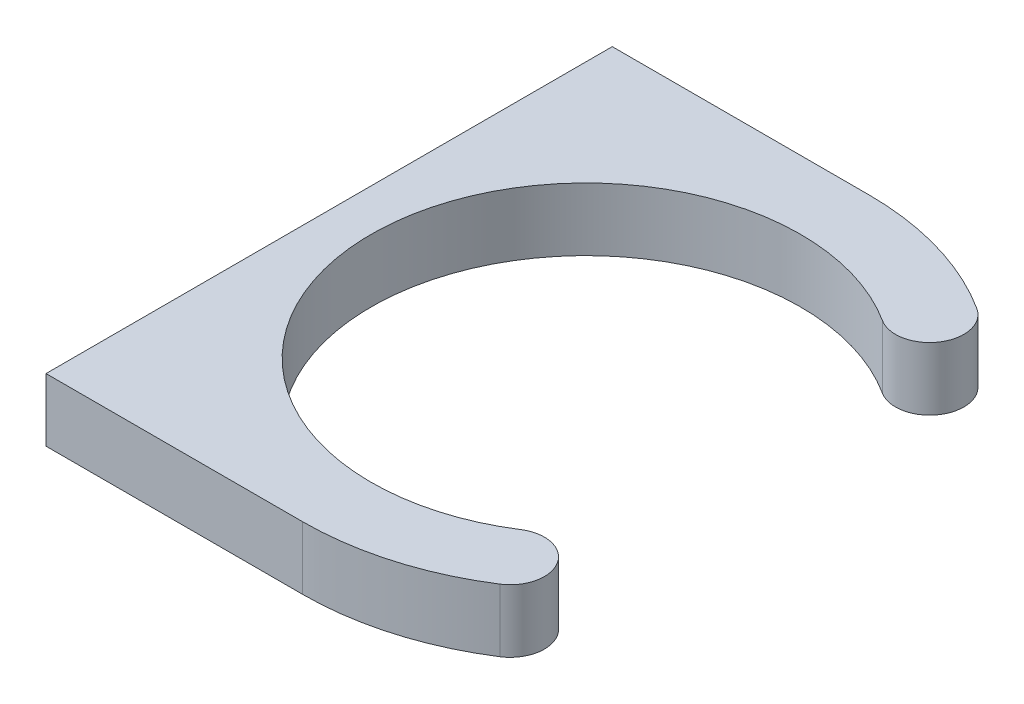
SolidWorks part; units mm, degrees
ref_plane "Front Plane" through (0, 0, 0) normal (0, 0, 1) x (1, 0, 0)
ref_plane "Top Plane" through (0, 0, 0) normal (0, 1, 0) x (1, 0, 0)
ref_plane "Right Plane" through (0, 0, 0) normal (1, 0, 0) x (0, 0, -1)
sketch "Sketch1" plane through (0, 0, 0) normal (0, 1, 0) x (1, 0, 0)
  line L0 (-38.862, 42.8625) -> (-38.862, -42.8625)
  line L1 (0, 42.8625) -> (-38.862, 42.8625)
  line L2 (0, -42.8625) -> (-38.862, -42.8625)
  circle A0 centre (0, 0) radius 32.512 construction
  arc A1 (23.0926, 36.1099) -> (0, 42.8625) centre (0, 0) ccw
  arc A2 (17.5161, 27.3901) -> (17.5161, -27.3901) centre (0, 0) ccw
  arc A3 (17.5161, 27.3901) -> (23.0926, 36.1099) centre (20.3043, 31.75) ccw
  arc A4 (17.5161, -27.3901) -> (23.0926, -36.1099) centre (20.3043, -31.75) cw
  arc A5 (0, -42.8625) -> (23.0926, -36.1099) centre (0, 0) ccw
  circle A6 centre (0, 0) radius 42.8625 construction
  point P9 (-32.512, 0)
  point P17 (38.862, 0)
  point P22 (-32.512, 0)
  dimension "D1" = 65.024
  dimension "D3" = 6.35
  dimension "D4" = 63.5
  dimension "D2" = 85.725
extrude "Boss-Extrude1" add sketch "Sketch1" along normal mid plane 9.525
sketch "Sketch2" plane through (-38.862, 0, 0) normal (-1, 0, 0) x (0, 0, 1)
  line L0 (-42.8625, 4.7625) -> (-42.8625, -4.7625) construction
  line L1 (42.8625, 4.7625) -> (42.8625, -4.7625) construction
  circle A0 centre (-38.1, 0) radius 1.3891
  circle A1 centre (38.1, 0) radius 1.3891
  dimension "D1" = 2.7781
  dimension "D2" = 4.7625
  dimension "D3" = 4.7625
extrude "Cut-Extrude1" cut sketch "Sketch2" against normal blind 25.4
